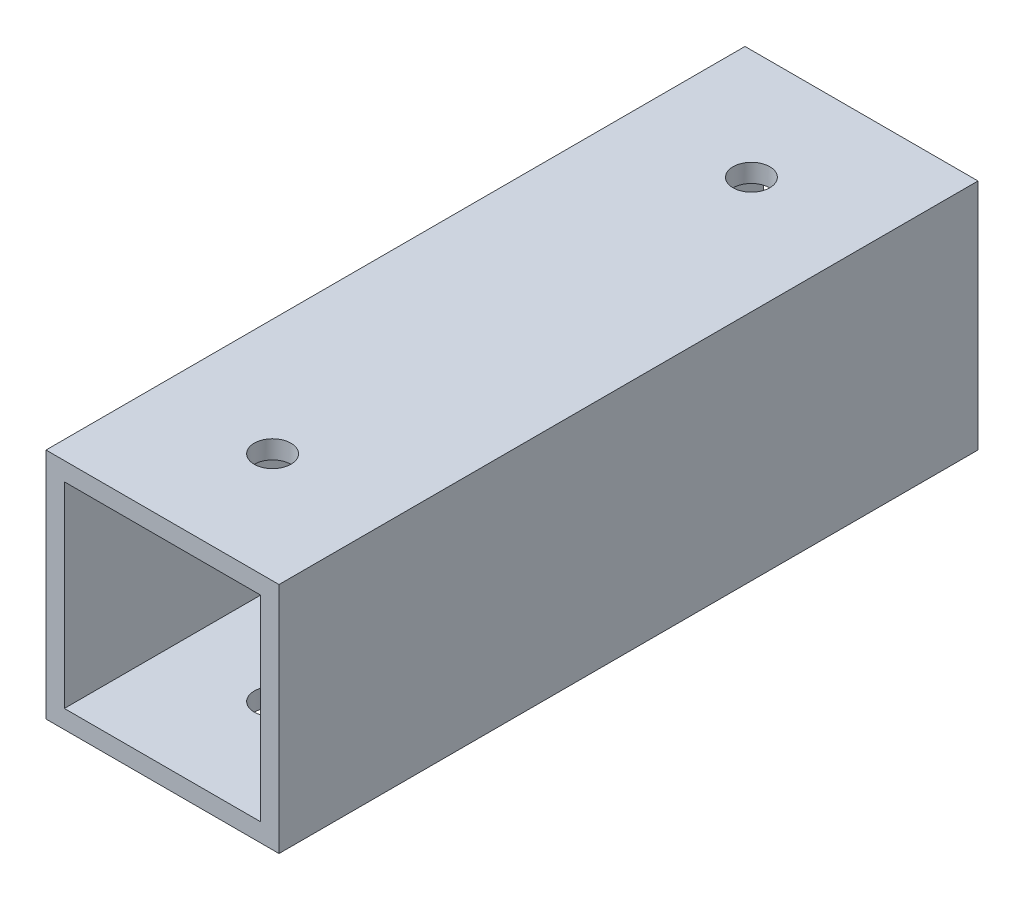
SolidWorks part; units mm, degrees
material "AISI 1020"
ref_plane "Front Plane" through (0, 0, 0) normal (0, 0, 1) x (1, 0, 0)
ref_plane "Top Plane" through (0, 0, 0) normal (0, 1, 0) x (1, 0, 0)
ref_plane "Right Plane" through (0, 0, 0) normal (1, 0, 0) x (0, 0, -1)
sketch "Sketch1" plane through (0, 0, 0) normal (0, 0, 1) x (1, 0, 0)
  line L1 (0, 0) -> (25.4, 0)
  line L2 (0, 0) -> (0, 25.4)
  line L3 (0, 25.4) -> (25.4, 25.4)
  line L4 (25.4, 0) -> (25.4, 25.4)
  line L5 (2, 23.4) -> (23.4, 23.4)
  line L6 (2, 23.4) -> (2, 2)
  line L7 (2, 2) -> (23.4, 2)
  line L8 (23.4, 23.4) -> (23.4, 2)
  dimension "D1" = 2
  dimension "D2" = 2
  dimension "D3" = 25.4
  dimension "D4" = 2
extrude "Boss-Extrude1" add sketch "Sketch1" along normal blind 76.2
sketch "Sketch3" plane through (0, 25.4, 0) normal (0, 1, 0) x (1, 0, 0)
  line L11 (12.7, -12) -> (12.7, 0) construction
  line L12 (25.4, 0) -> (0, 0) construction
  line L13 (12.7, -64.2) -> (12.7, -76.2) construction
  line L14 (25.4, -76.2) -> (0, -76.2) construction
  circle A0 centre (12.7, -12) radius 2
  circle A1 centre (12.7, -64.2) radius 2
  dimension "D2" = 4
  dimension "D1" = 12
extrude "Cut-Extrude2" cut sketch "Sketch3" against normal through all
